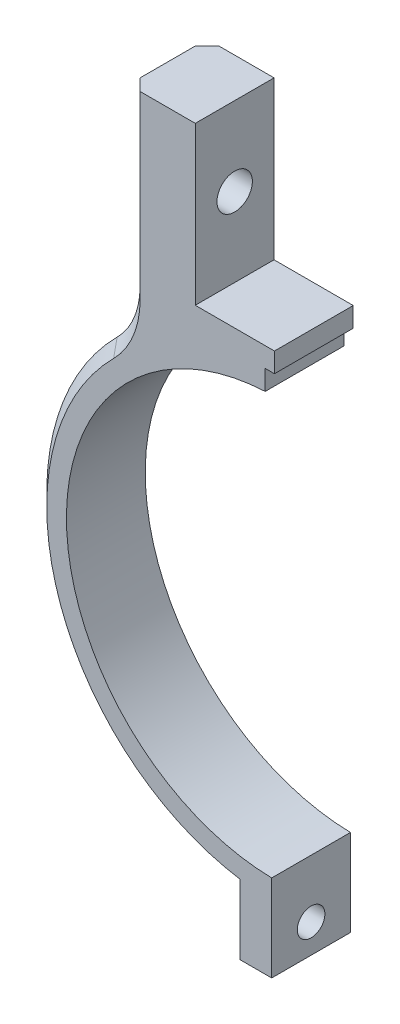
SolidWorks part; units mm, degrees
ref_plane "Ebene vorne" through (0, 0, 0) normal (0, 0, 1) x (1, 0, 0)
ref_plane "Ebene oben" through (0, 0, 0) normal (0, 1, 0) x (1, 0, 0)
ref_plane "Ebene rechts" through (0, 0, 0) normal (1, 0, 0) x (0, 0, -1)
sketch "Skizze1" plane through (0, 0, 0) normal (0, 0, 1) x (1, 0, 0)
  line L0 (0, 0) -> (0, 53.7291) construction
  line L14 (0, 0) -> (0, -44.1347) construction
  line L15 (0.5, -26.5453) -> (0.5, -30.5459)
  line L16 (-0.5, -26.5453) -> (-0.5, -30.5459)
  line L17 (0.5, -30.5459) -> (0.5, -37.5459)
  line L18 (0.5, -37.5459) -> (4.5, -37.5459)
  line L19 (4.5, -37.5459) -> (4.5, -30.2168)
  line L20 (-4.5, -37.5459) -> (-4.5, -30.2168)
  line L21 (-0.5, -37.5459) -> (-4.5, -37.5459)
  line L22 (-0.5, -30.5459) -> (-0.5, -37.5459)
  line L23 (-10.2, 31.55) -> (-10.2, 51.55)
  line L24 (-10.2, 51.55) -> (-18.7, 51.55)
  line L25 (-18.7, 51.55) -> (-18.7, 24.1581)
  line L26 (-10.2, 31.55) -> (10.2, 31.55)
  line L27 (0, 26.55) -> (12.0002, 26.55) construction
  line L28 (18.7, 51.55) -> (18.7, 24.1581)
  line L29 (10.2, 51.55) -> (18.7, 51.55)
  line L30 (10.2, 31.55) -> (10.2, 51.55)
  arc A0 (0.5, -26.5453) -> (-0.5, -26.5453) centre (0, 0) ccw
  arc A1 (-18.7, 24.1581) -> (-4.5, -30.2168) centre (0, 0) ccw
  arc A2 (4.5, -30.2168) -> (18.7, 24.1581) centre (0, 0) ccw
  point P10 (0, 33.5025)
  point P11 (0, 31.6594)
  point P17 (0, 31.55)
  point P18 (0, 39.6025)
  dimension "D1" = 53.1
  dimension "D2" = 4
  dimension "D3" = 20.4
  dimension "D4" = 20
  dimension "D5" = 5
  dimension "D6" = 8.5
  dimension "D10" = 1
  dimension "D11" = 4
  dimension "D12" = 7
extrude "Aufsatz-Linear austragen1" add sketch "Skizze1" along normal blind 10
sketch "Skizze2" plane through (-4.5, 0, 0) normal (-1, 0, 0) x (0, 0, 1)
  line L0 (0, -33.8813) -> (10, -33.8813) construction
  line L1 (0, -30.2168) -> (0, -37.5459) construction
  line L2 (10, -30.2168) -> (10, -37.5459) construction
  circle A0 centre (5, -33.8813) radius 1.75
  dimension "D1" = 3.5
extrude "Schnitt-Linear austragen1" cut sketch "Skizze2" against normal through all
sketch "Skizze3" plane through (0, 0, 10) normal (0, 0, 1) x (1, 0, 0)
  line L0 (-10.8174, 36.4205) -> (0, 26.8755)
  line L1 (0, 26.8755) -> (11.8484, 37.1414)
  line L2 (11.8484, 37.1414) -> (47.3746, 17.8863)
  line L3 (47.3746, 17.8863) -> (51.4546, -59.0738)
  line L4 (51.4546, -59.0738) -> (-81.1349, -43.2704)
  line L5 (-81.1349, -43.2704) -> (-40.9452, 68.8874)
  line L6 (-40.9452, 68.8874) -> (-10.8174, 36.4205)
extrude "Schnitt-Linear austragen2" [suppressed] cut sketch "Skizze3" against normal through all
sketch "Skizze4" plane through (-18.7, 0, 0) normal (-1, 0, 0) x (0, 0, 1)
  line L0 (5, 51.55) -> (5, 31.55) construction
  line L1 (10, 51.55) -> (0, 51.55) construction
  line L3 (10, 31.55) -> (0, 31.55) construction
  circle A0 centre (5, 41.55) radius 2.25
  dimension "D1" = 4.5
extrude "Schnitt-Linear austragen3" cut sketch "Skizze4" against normal through all
fillet "Verrundung1" radius 10 2 edges at (18.7, 24.1581, 5) (-18.7, 24.1581, 5)
sketch "Skizze5" plane through (-4.5, 0, 0) normal (-1, 0, 0) x (0, 0, 1)
  line L0 (5, -33.8813) -> (5, -27.6721) construction
  line L2 (2.225, -36.6563) -> (7.775, -36.6563)
  line L3 (2.225, -36.6563) -> (2.225, -31.1063)
  line L4 (2.225, -31.1063) -> (7.775, -31.1063)
  line L5 (7.775, -36.6563) -> (7.775, -31.1063)
  line L6 (2.225, -36.6563) -> (7.775, -31.1063) construction
  line L7 (2.225, -31.1063) -> (7.775, -36.6563) construction
  dimension "D1" = 5.55
extrude "Schnitt-Linear austragen4" [suppressed] cut sketch "Skizze5" against normal blind 2
sketch "Skizze6" plane through (0, 0, 0) normal (0, 0, 1) x (1, 0, 0)
  line L0 (0, 0) -> (0, 63.9135)
  line L1 (0, 63.9135) -> (40.0139, 63.9135)
  line L2 (40.0139, 63.9135) -> (48.3604, -54.8191)
  line L3 (48.3604, -54.8191) -> (0, -54.8191)
  line L4 (0, -54.8191) -> (0, 0)
extrude "Schnitt-Linear austragen5" cut sketch "Skizze6" along normal through all
chamfer "Fase1" distance 1.5 angle 45 6 edges at (-18.7, 40.0982, 0) (-18.7, 40.0982, 10) (-19.4594, 24.8238, 10) (-19.4594, 24.8238, 0) (-29.0064, -9.5882, 10) (-29.0064, -9.5882, 0)
sketch "Skizze7" plane through (0, 0, 10) normal (0, 0, 1) x (1, 0, 0)
  line L0 (0, 0) -> (0, 40.9199) construction
  line L1 (1.325, 29.05) -> (0, 29.05)
  line L2 (-1.325, 29.05) -> (-1.325, 25.1371)
  line L3 (-1.325, 25.1371) -> (1.325, 25.1371)
  line L4 (0, 26.55) -> (2.8167, 26.55) construction
  line L5 (1.325, 29.05) -> (1.325, 25.1371)
  line L6 (-0.15, 29.05) -> (-0.15, 31.55)
  line L7 (0, 31.55) -> (-10.2, 31.55) construction
  line L8 (-0.15, 31.55) -> (0, 31.55)
  line L9 (0, 31.55) -> (0, 29.05)
  line L10 (-0.15, 29.05) -> (-1.325, 29.05)
  point P11 (0, 25.1371)
  point P12 (0, 29.05)
  dimension "D1" = 2.5
  dimension "D2" = 2.65
  dimension "D3" = 0.15
extrude "Schnitt-Linear austragen6" cut sketch "Skizze7" against normal through all
